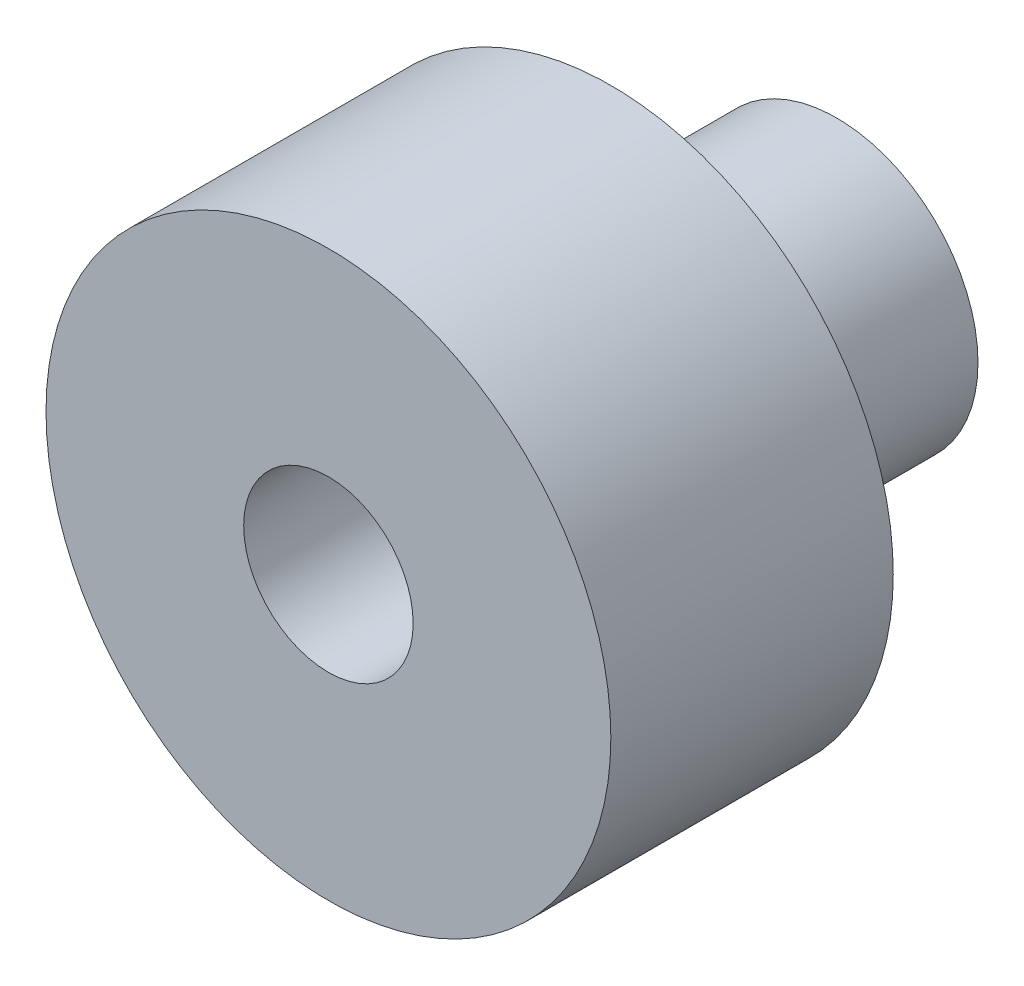
SolidWorks part; units mm, degrees
material "1060 Alloy"
ref_plane "Front" through (0, 0, 0) normal (0, 0, 1) x (1, 0, 0)
ref_plane "Top" through (0, 0, 0) normal (0, 1, 0) x (1, 0, 0)
ref_plane "Right" through (0, 0, 0) normal (1, 0, 0) x (0, 0, -1)
sketch "Sketch1" plane through (0, 0, 0) normal (0, 0, 1) x (1, 0, 0)
  circle A0 centre (0, 0) radius 10
  dimension "D1" = 20
extrude "Boss-Extrude1" add sketch "Sketch1" along normal blind 10
sketch "Sketch3" plane through (0, 0, 0) normal (0, 0, -1) x (-1, 0, 0)
  circle A0 centre (0, 0) radius 5
  dimension "D1" = 10
extrude "Boss-Extrude2" add sketch "Sketch3" along normal blind 8
sketch "Sketch4" plane through (0, 0, -8) normal (0, 0, -1) x (-1, 0, 0)
  circle A0 centre (0, 0) radius 3
  dimension "D1" = 6
extrude "Cut-Extrude1" cut sketch "Sketch4" against normal blind 27
sketch "Sketch5" plane through (0, 0, 0) normal (0, 1, 0) x (1, 0, 0)
  circle A0 centre (0, 5) radius 1.5
  dimension "D1" = 3
extrude "Cut-Extrude2" cut sketch "Sketch5" against normal blind 27
scale "Scale1" scale about centroid uniform scaling yes scale factor 3
scale "Scale2" scale about centroid uniform scaling yes scale factor 17
scale "Scale3" bodies to scale 113 scale about centroid uniform scaling yes scale factor 0.3
scale "Scale5" bodies to scale 114 scale about centroid uniform scaling yes scale factor 1.5
